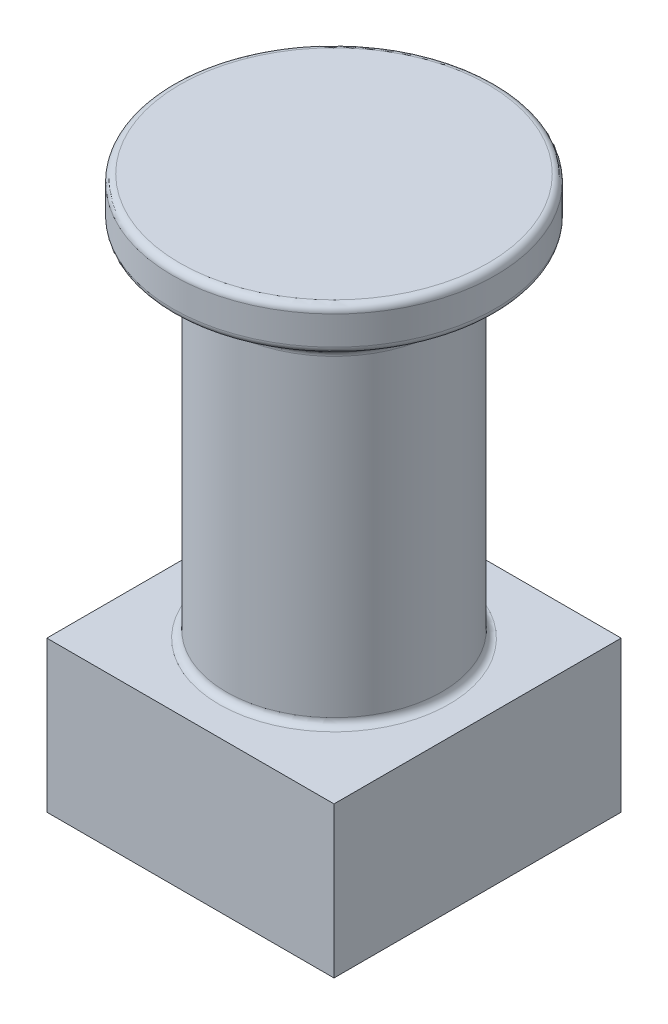
SolidWorks part; units mm, degrees
ref_plane "前视基准面" through (0, 0, 0) normal (0, 0, 1) x (1, 0, 0)
ref_plane "上视基准面" through (0, 0, 0) normal (0, 1, 0) x (1, 0, 0)
ref_plane "右视基准面" through (0, 0, 0) normal (1, 0, 0) x (0, 0, -1)
sketch "草图2" plane through (0, 0, 0) normal (0, 1, 0) x (1, 0, 0)
  line L1 (-20, 20) -> (20, 20)
  line L2 (-20, 20) -> (-20, -20)
  line L3 (-20, -20) -> (20, -20)
  line L4 (20, 20) -> (20, -20)
  line L5 (-20, 20) -> (20, -20) construction
  line L6 (-20, -20) -> (20, 20) construction
  point P0 (0, 0)
  dimension "D1" = 40
  dimension "D2" = 40
extrude "凸台-拉伸1" add sketch "草图2" along normal blind 21
sketch "草图3" plane through (0, 21, 0) normal (0, 1, 0) x (1, 0, 0)
  circle A0 centre (0, 0) radius 15
  dimension "D1" = 30
extrude "凸台-拉伸2" add sketch "草图3" along normal blind 50
sketch "草图4" plane through (0, 71, 0) normal (0, 1, 0) x (1, 0, 0)
  circle A0 centre (0, 0) radius 22.5
extrude "凸台-拉伸3" add sketch "草图4" along normal blind 6
chamfer "倒角1" distance 5 angle 45 1 edges at (0, 71, 15)
fillet "圆角1" radius 1 5 edges at (0, 71, 22.5) (0, 77, 22.5) (0, 71, 20) (0, 66, 15) (0, 21, 15)
